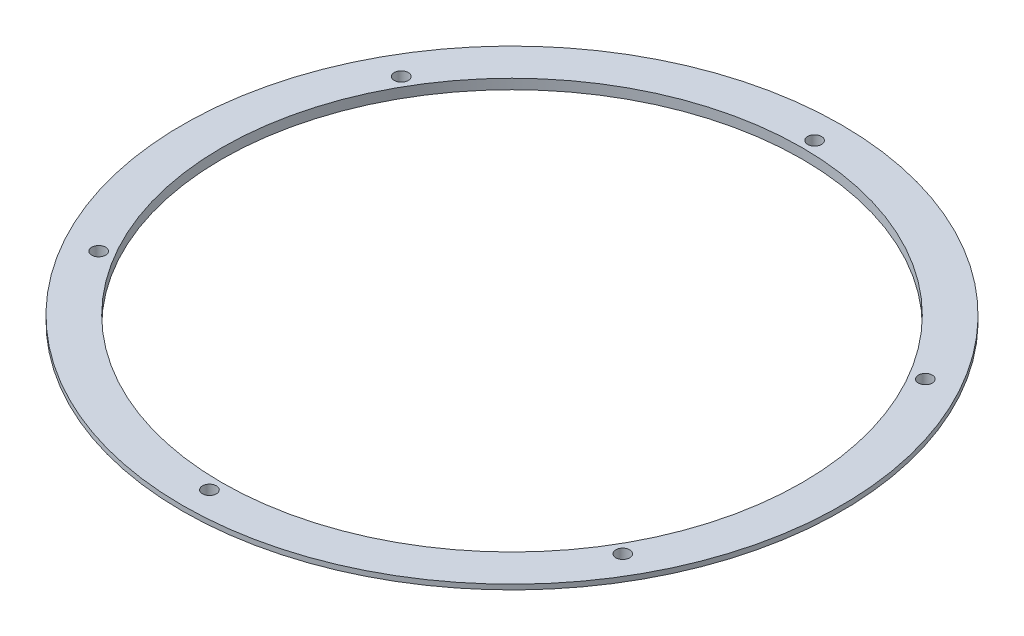
SolidWorks part; units mm, degrees
ref_plane "Front Plane" through (0, 0, 0) normal (0, 0, 1) x (1, 0, 0)
ref_plane "Top Plane" through (0, 0, 0) normal (0, 1, 0) x (1, 0, 0)
ref_plane "Right Plane" through (0, 0, 0) normal (1, 0, 0) x (0, 0, -1)
sketch "Sketch1" plane through (0, 0, 0) normal (0, 1, 0) x (1, 0, 0)
  line L0 (0, 154.5) -> (0, 0) construction
  line L1 (0, 160.85) -> (0, 148.15) construction
  line L2 (0, -55) -> (0, 55) construction
  circle A0 centre (0, 0) radius 154.5 construction
  circle A1 centre (0, 154.5) radius 3.556
  circle A2 centre (133.8009, 77.25) radius 3.556
  circle A3 centre (133.8009, -77.25) radius 3.556
  circle A4 centre (0, -154.5) radius 3.556
  circle A5 centre (-133.8009, -77.25) radius 3.556
  circle A6 centre (-133.8009, 77.25) radius 3.556
  circle A7 centre (0, 0) radius 160.85
  circle A8 centre (0, 0) radius 148.15
  point P17 (0, 0)
  point P20 (0, 154.5)
  dimension "D1" = 7.112
  dimension "D2" = 309
  dimension "D6" = 12.7
  dimension "D4" = 60
  dimension "D5" = 60
  dimension "D3" = 6
extrude "Boss-Extrude1" add sketch "Sketch1" along normal blind 5.08
sketch "Sketch2" plane through (0, 5.08, 0) normal (0, 1, 0) x (1, 0, 0)
  circle A0 centre (0, 0) radius 168.275
  circle A1 centre (0, 0) radius 160.85
  circle A2 centre (0, 0) radius 160.85 construction
  dimension "D1" = 336.55
extrude "Boss-Extrude2" add sketch "Sketch2" against normal blind 2.54
